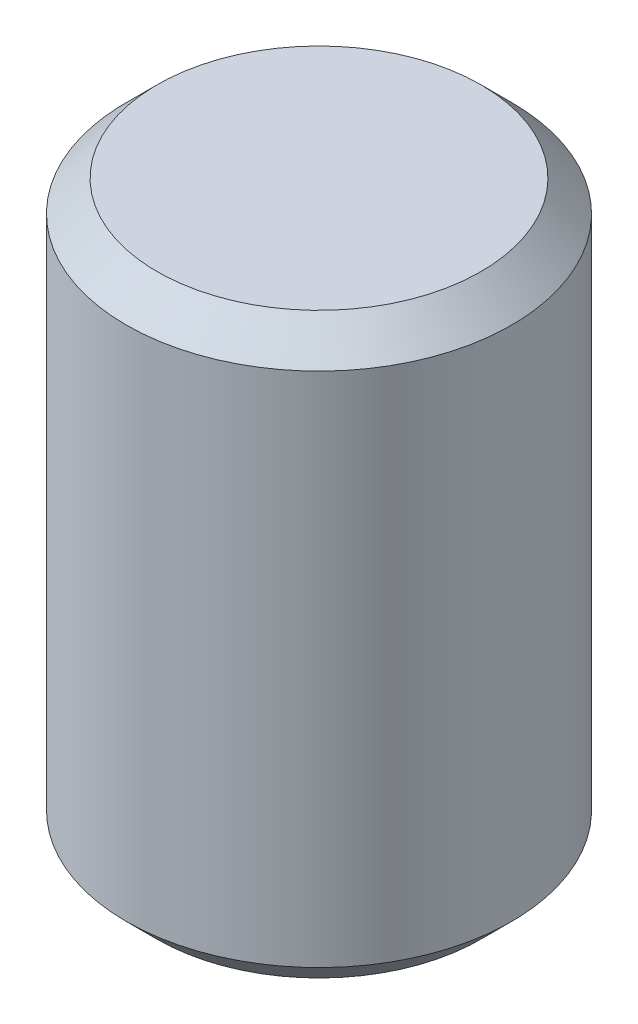
SolidWorks part; units mm, degrees
ref_plane "Front Plane" through (0, 0, 0) normal (0, 0, 1) x (1, 0, 0)
ref_plane "Top Plane" through (0, 0, 0) normal (0, 1, 0) x (1, 0, 0)
ref_plane "Right Plane" through (0, 0, 0) normal (1, 0, 0) x (0, 0, -1)
sketch "Sketch1" plane through (0, 0, 0) normal (0, 0, 1) x (1, 0, 0)
  line L0 (0, 1.4471) -> (0, -1.4471) construction
  line L1 (0, 4.7625) -> (3.175, 4.7625)
  line L2 (3.175, 4.7625) -> (3.175, -4.7625)
  line L3 (3.175, -4.7625) -> (0, -4.7625)
  line L4 (0, -4.7625) -> (0, 4.7625)
  dimension "D1" = 6.35
  dimension "D2" = 9.525
revolve "Revolve1" add sketch "Sketch1" angle 360 about L0
chamfer "Chamfer1" distance 0.508 angle 45 2 edges at (0, -4.7625, 3.175) (0, 4.7625, 3.175)
